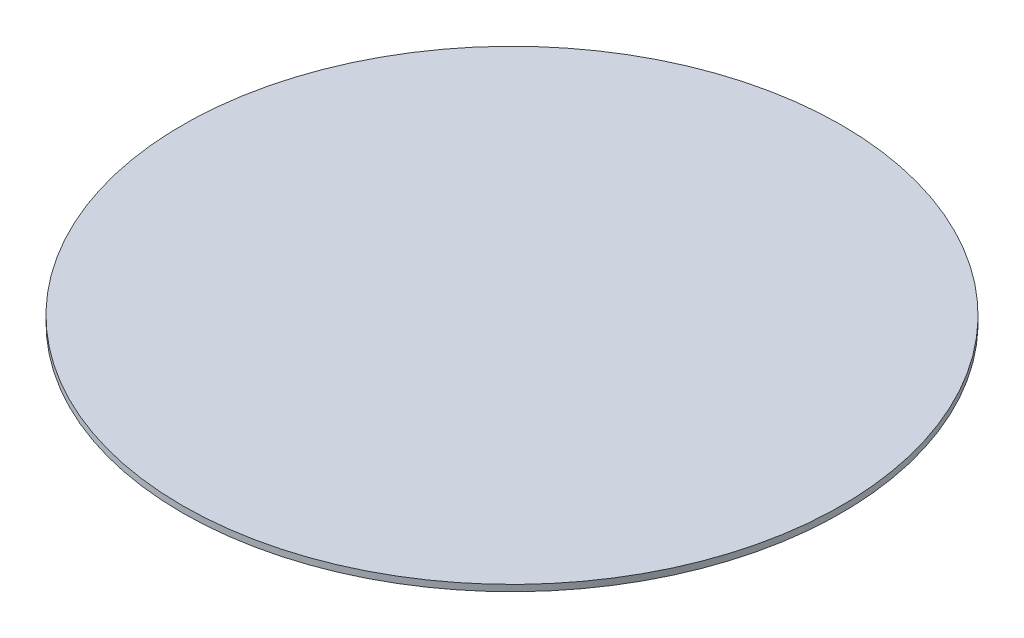
SolidWorks part; units mm, degrees
ref_plane "Front Plane" through (0, 0, 0) normal (0, 0, 1) x (1, 0, 0)
ref_plane "Top Plane" through (0, 0, 0) normal (0, 1, 0) x (1, 0, 0)
ref_plane "Right Plane" through (0, 0, 0) normal (1, 0, 0) x (0, 0, -1)
sketch "Sketch1" plane through (0, 0, 0) normal (0, 1, 0) x (1, 0, 0)
  circle A0 centre (0, 0) radius 165.1
  dimension "D1" = 330.2
extrude "Boss-Extrude1" add sketch "Sketch1" along normal blind 3.175
